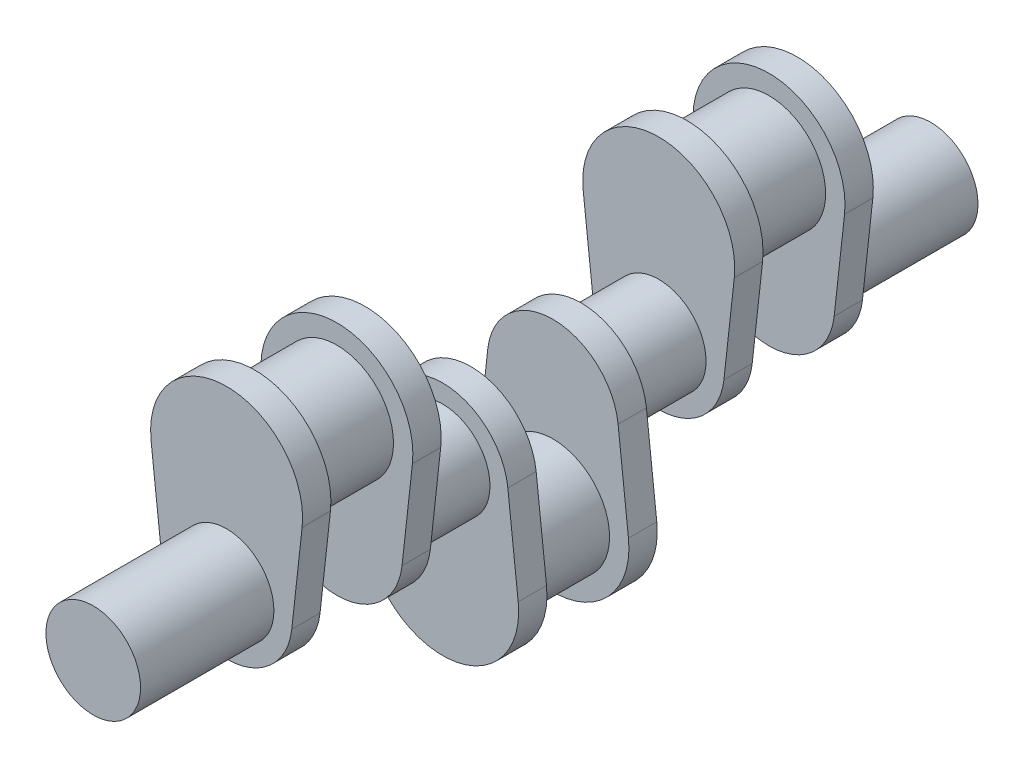
SolidWorks part; units mm, degrees
ref_plane "Front Plane" through (0, 0, 0) normal (0, 0, 1) x (1, 0, 0)
ref_plane "Top Plane" through (0, 0, 0) normal (0, 1, 0) x (1, 0, 0)
ref_plane "Right Plane" through (0, 0, 0) normal (1, 0, 0) x (0, 0, -1)
sketch "Sketch1" plane through (0, 0, 0) normal (0, 0, 1) x (1, 0, 0)
  circle A0 centre (0, 0) radius 31.75
extrude "Boss-Extrude1" add sketch "Sketch1" along normal blind 89.5
sketch "Sketch2" plane through (0, 0, 89.5) normal (0, 0, 1) x (1, 0, 0)
  line L0 (-50.6892, 57.878) -> (-43.7318, -4.8504)
  line L1 (43.7318, -4.8504) -> (50.6892, 57.878)
  arc A0 (50.6892, 57.878) -> (-50.6892, 57.878) centre (0, 63.5) ccw
  arc A1 (-43.7318, -4.8504) -> (43.7318, -4.8504) centre (0, 0) ccw
  dimension "D1" = 63.5
extrude "Boss-Extrude2" add sketch "Sketch2" along normal blind 19
sketch "Sketch3" plane through (0, 0, 108.5) normal (0, 0, 1) x (1, 0, 0)
  circle A0 centre (0, 63.5) radius 38
extrude "Boss-Extrude3" add sketch "Sketch3" along normal blind 55
sketch "Sketch5" plane through (0, 0, 163.5) normal (0, 0, 1) x (1, 0, 0)
  line L2 (-50.6892, 57.878) -> (-43.7318, -4.8504)
  line L3 (43.7318, -4.8504) -> (50.6892, 57.878)
  line L4 (-50.6892, 57.878) -> (-43.7318, -4.8504)
  line L5 (43.7318, -4.8504) -> (50.6892, 57.878)
  arc A2 (50.6892, 57.878) -> (-50.6892, 57.878) centre (0, 63.5) ccw
  arc A3 (-43.7318, -4.8504) -> (43.7318, -4.8504) centre (0, 0) ccw
  arc A4 (50.6892, 57.878) -> (-50.6892, 57.878) centre (0, 63.5) ccw
  arc A5 (-43.7318, -4.8504) -> (43.7318, -4.8504) centre (0, 0) ccw
  dimension "D1" = 0
extrude "Boss-Extrude4" add sketch "Sketch5" along normal blind 19
sketch "Sketch6" plane through (0, 0, 182.5) normal (0, 0, 1) x (1, 0, 0)
  circle A1 centre (0, 0) radius 31.75
  circle A2 centre (0, 0) radius 31.75
  dimension "D1" = 0
extrude "Boss-Extrude5" add sketch "Sketch6" along normal blind 52
sketch "Sketch7" plane through (0, 0, 234.5) normal (0, 0, 1) x (1, 0, 0)
  line L4 (50.6892, -57.878) -> (43.7318, 4.8504)
  line L5 (-43.7318, 4.8504) -> (-50.6892, -57.878)
  arc A4 (-50.6892, -57.878) -> (50.6892, -57.878) centre (0, -63.5) ccw
  arc A5 (43.7318, 4.8504) -> (-43.7318, 4.8504) centre (0, 0) ccw
extrude "Boss-Extrude6" add sketch "Sketch7" along normal blind 19
sketch "Sketch8" plane through (0, 0, 253.5) normal (0, 0, 1) x (1, 0, 0)
  circle A0 centre (0, -63.5) radius 38
extrude "Boss-Extrude7" add sketch "Sketch8" along normal blind 27.5
ref_plane "Plane1" through (0, 0, 281) normal (0, 0, 1) x (1, 0, 0)
mirror "Mirror3" about plane through (0, 0, 281) normal (0, 0, 1) of bodies 107
